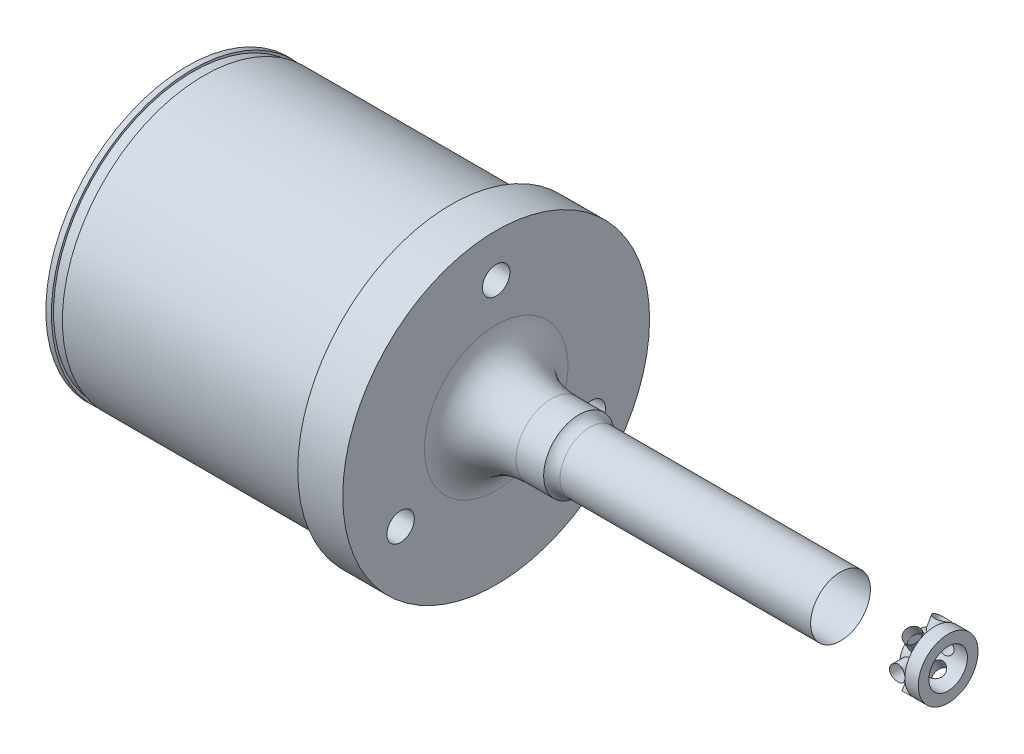
SolidWorks part; units mm, degrees
material "AISI 4340 Steel, normalized"
ref_plane "Front Plane" through (0, 0, 0) normal (0, 0, 1) x (1, 0, 0)
ref_plane "Top Plane" through (0, 0, 0) normal (0, 1, 0) x (1, 0, 0)
ref_plane "Right Plane" through (0, 0, 0) normal (1, 0, 0) x (0, 0, -1)
sketch "Sketch1" plane through (0, 0, 0) normal (0, 0, 1) x (1, 0, 0)
  line L0 (-132.526, 0) -> (143.2472, 0) construction
  line L1 (0, 16.51) -> (0, 35.306)
  line L2 (0, 35.306) -> (-10.3632, 35.306)
  line L3 (-10.3632, 35.306) -> (-10.3632, 32.766)
  line L4 (-10.3632, 32.766) -> (-71.12, 32.766)
  line L5 (-71.12, 32.766) -> (-71.12, 0)
  line L6 (-71.12, 0) -> (104.013, 0)
  line L7 (104.013, 0) -> (104.013, 6.8834)
  line L8 (104.013, 6.8834) -> (21.5708, 6.8834)
  line L9 (19.05, 8.128) -> (12.7, 8.128)
  arc A0 (21.5708, 6.8834) -> (19.05, 8.128) centre (21.5708, 10.0584) cw
  ellipse E0 centre (12.7, 16.51) end of major axis (25.4, 16.51) minor radius 8.382 (0, 16.51) -> (12.7, 8.128) ccw
  dimension "D9" = 3.175
  dimension "D1" = 13.7668
  dimension "D2" = 10.3632
  dimension "D3" = 65.532
  dimension "D4" = 70.612
  dimension "D5" = 16.256
  dimension "D6" = 104.013
  dimension "D7" = 71.12
  dimension "D8" = 33.02
  dimension "D10" = 12.7
  dimension "D11" = 6.35
revolve "Base Revolve" add sketch "Sketch1" angle 360 about L0
ref_axis "Centerline" through (116.6455, 0, 0) along (-1, 0, 0)
ref_plane "Thread Start" through (100.9396, 0, 0) normal (1, 0, 0) x (0, 0, -1)
ref_plane "Thread End" through (79.248, 0, 0) normal (1, 0, 0) x (0, 0, -1)
split line "Thread Split End"
split line "Thread Split Start"
sketch "Sketch4" plane through (0, 0, 0) normal (1, 0, 0) x (0, 0, -1)
  line L0 (0, 25.4) -> (0, 0) construction
  circle A0 centre (0, 25.4) radius 3.1623
  dimension "D1" = 6.3246
  dimension "D2" = 25.4
extrude "Dowel Pin Hole" cut sketch "Sketch4" against normal through all
pattern_circular "CirPattern1" count 3 over 360 about axis through (0, 0, 0) along (1, 0, 0) of "Dowel Pin Hole"
sketch "Sketch9" plane through (0, 0, 0) normal (0, 0, 1) x (1, 0, 0)
  line L0 (100.9396, 6.8834) -> (100.9396, -6.8834) construction
  line L1 (100.9396, 6.8834) -> (100.9396, -6.8834) construction
  line L2 (116.6455, 0) -> (-95.9774, 0) construction
  circle A0 centre (99.1616, 0) radius 1.778
  dimension "D1" = 3.556
extrude "Cotter Pin Hole" cut sketch "Sketch9" against normal mid plane 55.88
pattern_circular "CirPattern3" count 3 over 360 about axis through (116.6455, 0, 0) along (-1, 0, 0) of "Cotter Pin Hole"
sketch "Sketch10" plane through (104.013, 0, 0) normal (1, 0, 0) x (0, 0, -1)
  circle A0 centre (0, 0) radius 4.445
  circle A1 centre (0, 0) radius 6.8834 construction
  dimension "D1" = 8.89
extrude "Shank Tip Relief" cut sketch "Sketch10" against normal blind 6.731
sketch "Sketch14" plane through (0, 0, 0) normal (0, 0, 1) x (1, 0, 0)
  line L0 (0, 35.306) -> (0, 28.5623)
  line L1 (0, 22.2377) -> (0, 16.51)
  line L2 (0, -16.51) -> (0, -35.306)
  line L3 (0, 34.6404) -> (0, -35.306) construction
  line L4 (-5.08, 0) -> (-5.08, 22.987)
  line L5 (-5.08, 22.987) -> (-30.48, 30.607)
  line L6 (-30.48, 30.607) -> (-71.12, 30.607)
  line L7 (-71.12, 32.766) -> (-71.12, -32.766) construction
  line L8 (-71.12, 30.607) -> (-71.12, 0)
  line L9 (-71.12, 0) -> (-5.08, 0)
  line L11 (-71.12, 0) -> (-87.1146, 0) construction
  dimension "D1" = 5.08
  dimension "D2" = 7.62
  dimension "D3" = 25.4
  dimension "D4" = 61.214
revolve "Inside Cut" cut sketch "Sketch14" angle 360 about axis through (116.6455, 0, 0) along (-1, 0, 0)
sketch "Sketch7" plane through (0, 0, 0) normal (0, 0, 1) x (1, 0, 0)
  line L0 (-5.08, -22.987) -> (-5.08, 22.2377)
  line L1 (-5.08, 0) -> (-5.08, 13.2859)
  line L3 (-5.08, 0) -> (-2.032, 0)
  line L4 (-5.08, 0) -> (-32.512, 0) construction
  arc A0 (-2.032, 0) -> (-5.08, 13.2859) centre (-32.512, 0) ccw
  dimension "D1" = 30.48
  dimension "D2" = 3.048
revolve "Axle Relief" cut sketch "Sketch7" angle 360 about L4
sketch "Sketch11" plane through (0, 0, 0) normal (0, 0, 1) x (1, 0, 0)
  line L0 (-10.3632, -35.306) -> (-10.3632, -32.766)
  line L1 (-10.3632, 32.766) -> (-10.3632, 35.306)
  line L2 (-10.3632, 34.3829) -> (-10.3632, 35.306)
  line L3 (-10.3632, -35.306) -> (-10.3632, -32.766)
  line L4 (-10.922, 32.5183) -> (-67.31, 32.5183)
  line L6 (-82.412, 0) -> (108.1661, 0) construction
  line L7 (116.6455, 0) -> (-95.9774, 0) construction
  line L8 (-10.3632, 35.306) -> (0, 35.306)
  line L9 (0, -35.306) -> (-10.3632, -35.306)
  line L11 (-10.3632, 35.306) -> (0, 35.306) construction
  line L12 (-10.3632, 32.766) -> (-10.3632, 32.6858) construction
  line L14 (-10.3632, 35.306) -> (-10.3632, -35.306) construction
  line L15 (-71.12, -32.766) -> (-71.12, -30.607)
  line L16 (-71.12, 30.607) -> (-71.12, 32.766)
  line L17 (-71.12, 35.306) -> (-71.12, 32.5183)
  line L18 (-71.12, 32.766) -> (-71.12, -32.766) construction
  line L19 (-71.12, 32.5183) -> (-69.85, 32.5183)
  line L20 (-69.85, 32.5183) -> (-69.85, 32.0104)
  line L21 (-69.85, 32.0104) -> (-67.31, 32.0104)
  line L22 (-67.31, 32.5183) -> (-67.31, 32.0104)
  line L23 (-71.12, 35.306) -> (-10.3632, 35.306)
  arc A0 (-10.922, 32.5183) -> (-10.3632, 34.3829) centre (-10.922, 33.5344) ccw
  dimension "D1" = 1.016
  dimension "D2" = 0.5588
  dimension "D3" = 65.0367
  dimension "D4" = 0.0802
  dimension "D5" = 1.27
  dimension "D6" = 2.54
  dimension "D7" = 0.508
revolve "Final Cut" cut sketch "Sketch11" angle 360 about axis through (116.6455, 0, 0) along (-1, 0, 0)
